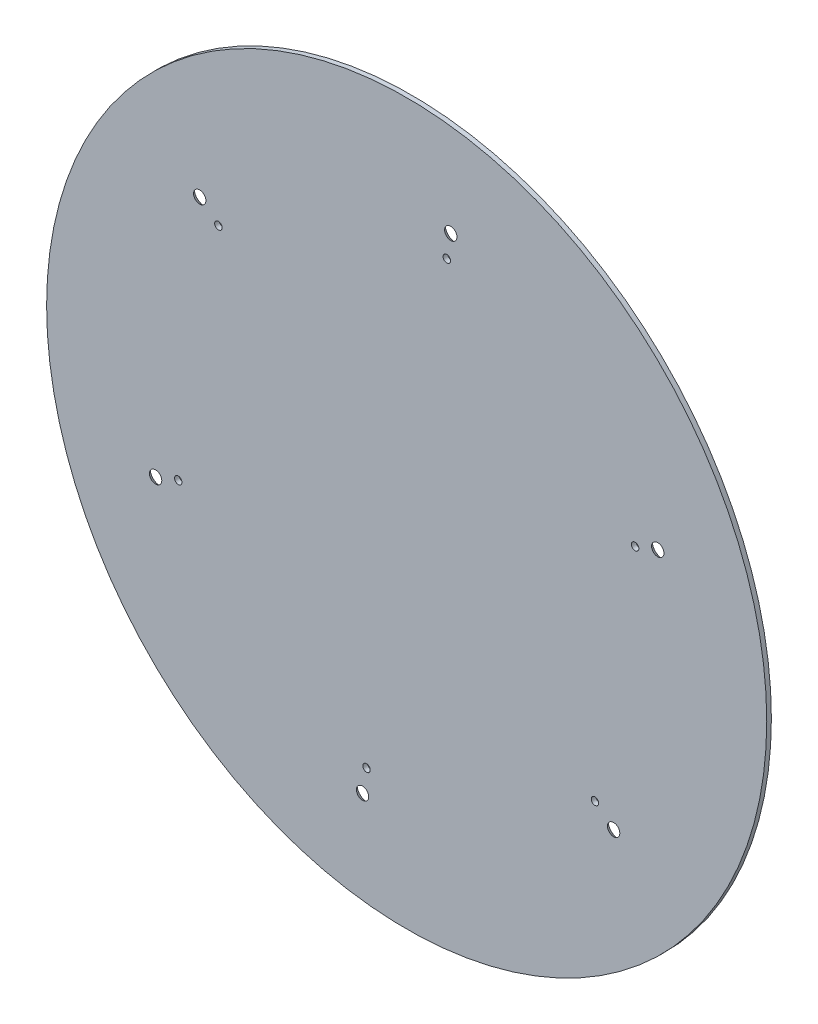
SolidWorks part; units mm, degrees
ref_plane "Front Plane" through (0, 0, 0) normal (0, 0, 1) x (1, 0, 0)
ref_plane "Top Plane" through (0, 0, 0) normal (0, 1, 0) x (1, 0, 0)
ref_plane "Right Plane" through (0, 0, 0) normal (1, 0, 0) x (0, 0, -1)
sketch "Sketch1" plane through (0, 0, 0) normal (0, 0, 1) x (1, 0, 0)
  circle A0 centre (0, 0) radius 155
extrude "Boss-Extrude1" add sketch "Sketch1" along normal blind 2 contours A0
sketch "Sketch2" plane through (0, 0, 2) normal (0, 0, 1) x (1, 0, 0)
  circle A0 centre (18.9812, 113.8384) radius 3.175
  circle A1 centre (108.0776, 40.481) radius 3.175
  circle A2 centre (-89.0885, 73.3669) radius 3.175
  circle A3 centre (-108.0776, -40.481) radius 3.175
  circle A4 centre (-18.9812, -113.8384) radius 3.175
  circle A5 centre (89.0885, -73.3669) radius 3.175
sketch "Sketch3" plane through (0, 0, 2) normal (0, 0, 1) x (1, 0, 0)
  circle A0 centre (17.2802, 103.5683) radius 1.6
  circle A1 centre (-81.0527, 66.7492) radius 1.6
  circle A2 centre (-98.3329, -36.8191) radius 1.6
  circle A3 centre (-17.2802, -103.5683) radius 1.6
  circle A4 centre (81.0527, -66.7492) radius 1.6
  circle A5 centre (98.3329, 36.8191) radius 1.6
extrude "Cut-Extrude2" cut sketch "Sketch3" against normal blind 10
hole_wizard "CSK for #8 Flat Head Machine Screw (100)1" positions "Sketch6" profile "Sketch7" countersink size "#8" standard "ANSI Inch"
sketch "Sketch6" plane through (0, 0, 0) normal (0, 0, -1) x (-1, 0, 0)
  point P0 (-18.9812, 113.8384)
  point P2 (89.0885, 73.3669)
  point P4 (108.0776, -40.481)
  point P6 (-108.0776, 40.481)
  point P8 (-89.0885, -73.3669)
  point P10 (18.9812, -113.8384)
sketch "Sketch7" plane through (18.9812, 113.8384, 0) normal (1, 0, 0) x (0, 1, 0)
  line L0 (0, 0) -> (0, 12.0607)
  line L1 (0, 12.0607) -> (2.2479, 10.71)
  line L2 (2.2479, 10.71) -> (2.2479, 2.4645)
  line L3 (2.2479, 2.4645) -> (4.3903, 0)
  line L5 (4.3903, 0) -> (0, 0)
  line L6 (-2.2479, 2.4645) -> (-4.3903, 0) construction
  line L10 (0, 12.0607) -> (-2.2479, 10.71) construction
  line L11 (0, -6.35) -> (0, 107.95) construction
  dimension "Hole Dia." = 4.4958
  dimension "Hole Depth" = 10.71
  dimension "Near C'Sink Dia." = 8.7805
  dimension "Near C'Sink Angle" = 82
  dimension "Drill Angle" = 118
